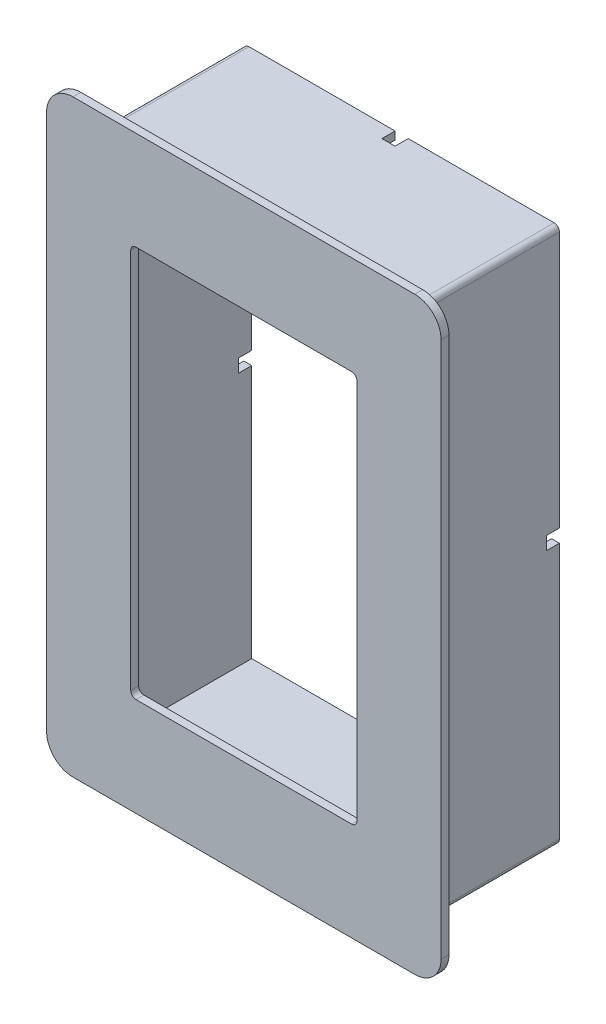
SolidWorks part; units mm, degrees
ref_plane "Plano frontal" through (0, 0, 0) normal (0, 0, 1) x (1, 0, 0)
ref_plane "Plano superior" through (0, 0, 0) normal (0, 1, 0) x (1, 0, 0)
ref_plane "Plano direito" through (0, 0, 0) normal (1, 0, 0) x (0, 0, -1)
sketch "Esboço1" plane through (0, 0, 0) normal (0, 0, 1) x (1, 0, 0)
  line L5 (-32.6754, 150.8202) -> (87.3246, 150.8202)
  line L6 (-32.6754, 150.8202) -> (-32.6754, -53.1798)
  line L7 (-32.6754, -53.1798) -> (87.3246, -53.1798)
  line L8 (87.3246, 150.8202) -> (87.3246, -53.1798)
  dimension "D1" = 120
  dimension "D2" = 204
extrude "Ressalto-extrusão1" add sketch "Esboço1" along normal blind 60
sketch "Esboço2" plane through (0, 0, 0) normal (0, 0, -1) x (-1, 0, 0)
  line L0 (32.6754, -53.1798) -> (-87.3246, -53.1798) construction
  line L1 (29.6754, -50.1798) -> (-84.3246, -50.1798)
  line L2 (29.6754, -50.1798) -> (29.6754, 147.8202)
  line L3 (29.6754, 147.8202) -> (-84.3246, 147.8202)
  line L4 (-84.3246, -50.1798) -> (-84.3246, 147.8202)
  line L5 (-87.3246, -53.1798) -> (-87.3246, 150.8202) construction
  line L6 (32.6754, 150.8202) -> (32.6754, -53.1798) construction
  line L7 (-87.3246, 150.8202) -> (32.6754, 150.8202) construction
  dimension "D1" = 3
  dimension "D2" = 3
  dimension "D3" = 3
  dimension "D4" = 3
extrude "Corte-extrusão1" cut sketch "Esboço2" against normal blind 57
sketch "Esboço4" plane through (0, 0, 60) normal (0, 0, 1) x (1, 0, 0)
  line L1 (-15.6754, 123.3202) -> (70.3246, 123.3202)
  line L2 (-15.6754, 123.3202) -> (-15.6754, -25.6798)
  line L3 (-15.6754, -25.6798) -> (70.3246, -25.6798)
  line L4 (70.3246, 123.3202) -> (70.3246, -25.6798)
  line L5 (-32.6754, -53.1798) -> (87.3246, -53.1798) construction
  line L7 (-32.6754, 150.8202) -> (-32.6754, -53.1798) construction
  dimension "D1" = 86
  dimension "D2" = 27.5
  dimension "D3" = 149
  dimension "D4" = 17
extrude "Corte-extrusão2" cut sketch "Esboço4" against normal blind 45 contours L2 L3 L4 L1
sketch "Esboço7" plane through (87.3246, 0, 0) normal (1, 0, 0) x (0, 0, -1)
  line L0 (-60, -53.1798) -> (-60, 150.8202) construction
  line L1 (-60, 150.8202) -> (-57, 150.8202)
  line L2 (-60, 150.8202) -> (-60, -53.1798)
  line L3 (-60, -53.1798) -> (-57, -53.1798)
  line L4 (-57, 150.8202) -> (-57, -53.1798)
  line L5 (-60, 150.8202) -> (0, 150.8202) construction
  line L6 (-60, -53.1798) -> (0, -53.1798) construction
  dimension "D1" = 3
extrude "Ressalto-extrusão2" add sketch "Esboço7" along normal blind 15 contours L2 L3 L4 L1
sketch "Esboço12" plane through (-32.6754, 0, 0) normal (-1, 0, 0) x (0, 0, 1)
  line L0 (60, -53.1798) -> (0, -53.1798) construction
  line L1 (60, 150.8202) -> (57, 150.8202)
  line L2 (60, 150.8202) -> (60, -53.1798)
  line L3 (60, -53.1798) -> (57, -53.1798)
  line L4 (57, 150.8202) -> (57, -53.1798)
  dimension "D1" = 3
extrude "Ressalto-extrusão3" add sketch "Esboço12" along normal blind 15 contours L2 L3 L4 L1
sketch "Esboço13" plane through (0, 150.8202, 0) normal (0, 1, 0) x (1, 0, 0)
  line L1 (102.3246, -57) -> (-47.6754, -57)
  line L2 (102.3246, -57) -> (102.3246, -60)
  line L3 (102.3246, -60) -> (-47.6754, -60)
  line L4 (-47.6754, -57) -> (-47.6754, -60)
extrude "Ressalto-extrusão4" add sketch "Esboço13" along normal blind 10 contours L3 L4 L1 L2
sketch "Esboço14" plane through (0, -53.1798, 0) normal (0, -1, 0) x (1, 0, 0)
  line L1 (-47.6754, 60) -> (102.3246, 60)
  line L2 (-47.6754, 60) -> (-47.6754, 57)
  line L3 (-47.6754, 57) -> (102.3246, 57)
  line L4 (102.3246, 60) -> (102.3246, 57)
extrude "Ressalto-extrusão5" add sketch "Esboço14" along normal blind 10
fillet "Filete1" radius 10 1 edges at (102.3246, 160.8202, 58.5)
sketch "Esboço15" plane through (0, 0, 0) normal (0, 0, -1) x (-1, 0, 0)
  line L0 (32.6754, 150.8202) -> (32.6754, -53.1798) construction
  line L1 (32.6754, 51.3202) -> (29.6754, 51.3202)
  line L2 (32.6754, 51.3202) -> (32.6754, 46.3202)
  line L3 (32.6754, 46.3202) -> (29.6754, 46.3202)
  line L4 (29.6754, 51.3202) -> (29.6754, 46.3202)
  line L5 (29.6754, -50.1798) -> (29.6754, 147.8202) construction
  line L6 (29.6754, 147.8202) -> (-84.3246, 147.8202) construction
  line L7 (-24.8246, 147.8202) -> (-29.8246, 147.8202)
  line L8 (-24.8246, 147.8202) -> (-24.8246, 150.8202)
  line L9 (-24.8246, 150.8202) -> (-29.8246, 150.8202)
  line L10 (-29.8246, 147.8202) -> (-29.8246, 150.8202)
  line L11 (-87.3246, 150.8202) -> (32.6754, 150.8202) construction
  line L12 (32.6754, -53.1798) -> (-87.3246, -53.1798) construction
  line L13 (-24.8246, -53.1798) -> (-29.8246, -53.1798)
  line L14 (-24.8246, -53.1798) -> (-24.8246, -50.1798)
  line L15 (-24.8246, -50.1798) -> (-29.8246, -50.1798)
  line L16 (-29.8246, -53.1798) -> (-29.8246, -50.1798)
  line L18 (-84.3246, 147.8202) -> (-84.3246, -50.1798) construction
  line L19 (-84.3246, 51.3202) -> (-87.3246, 51.3202)
  line L20 (-84.3246, 51.3202) -> (-84.3246, 46.3202)
  line L21 (-84.3246, 46.3202) -> (-87.3246, 46.3202)
  line L22 (-87.3246, 51.3202) -> (-87.3246, 46.3202)
  line L23 (-87.3246, -53.1798) -> (-87.3246, 150.8202) construction
  dimension "D1" = 5
  dimension "D2" = 5
  dimension "D3" = 5
  dimension "D4" = 5
  dimension "D5" = 57.5
  dimension "D6" = 99.5
  dimension "D7" = 99.5
  dimension "D8" = 57.5
extrude "Corte-extrusão4" cut sketch "Esboço15" against normal blind 5 contours L9 L10 L7 L8 | L2 L3 L4 L1 | L13 L16 L15 L14 | L22 L21 L20 L19
fillet "Filete2" radius 10 1 edges at (-47.6754, 160.8202, 58.5)
fillet "Filete3" radius 10 1 edges at (102.3246, -63.1798, 58.5)
fillet "Filete4" radius 10 1 edges at (-47.6754, -63.1798, 58.5)
fillet "Filete5" radius 2 1 edges
fillet "Filete6" radius 2 3 edges
fillet "Filete8" radius 2 4 edges at (70.3246, 123.3202, 58.5) (70.3246, -25.6798, 58.5) (-15.6754, -25.6798, 58.5) (-15.6754, 123.3202, 58.5)
